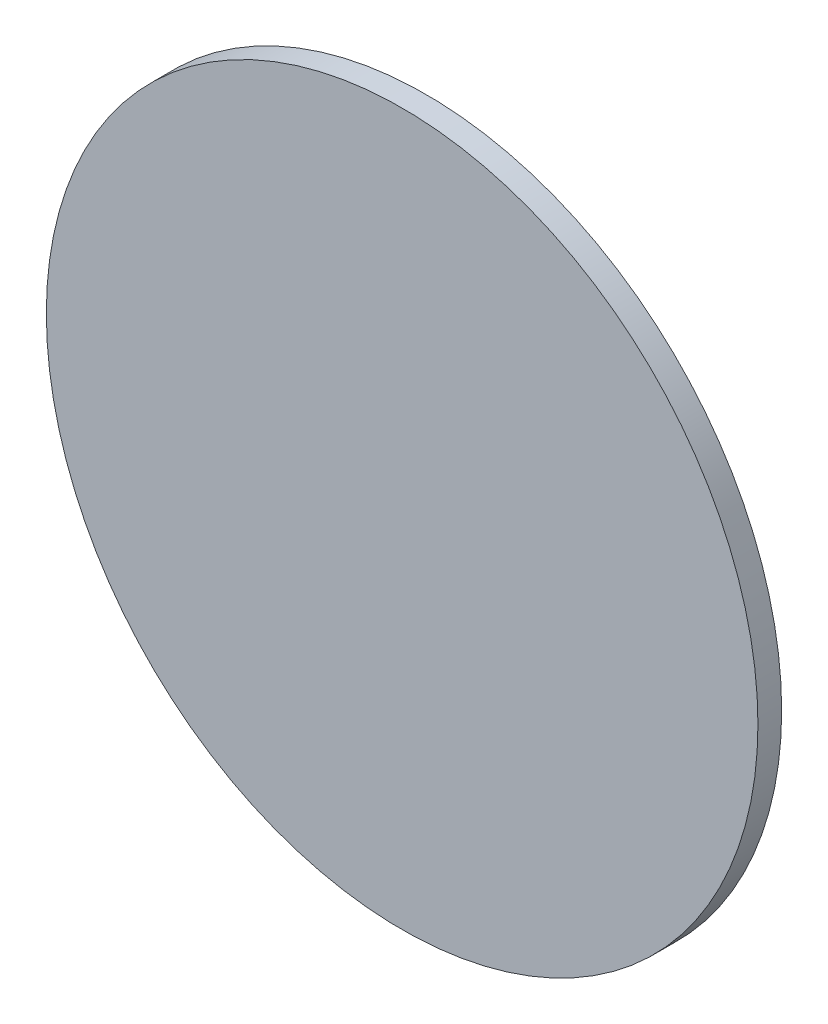
SolidWorks part; units mm, degrees
ref_plane "Front Plane" through (0, 0, 0) normal (0, 0, 1) x (1, 0, 0)
ref_plane "Top Plane" through (0, 0, 0) normal (0, 1, 0) x (1, 0, 0)
ref_plane "Right Plane" through (0, 0, 0) normal (1, 0, 0) x (0, 0, -1)
sketch "Sketch1" plane through (0, 0, 0) normal (0, 0, 1) x (1, 0, 0)
  circle A0 centre (0, 0) radius 38.1
  dimension "D1" = 76.2
extrude "Boss-Extrude1" add sketch "Sketch1" along normal blind 2.54
